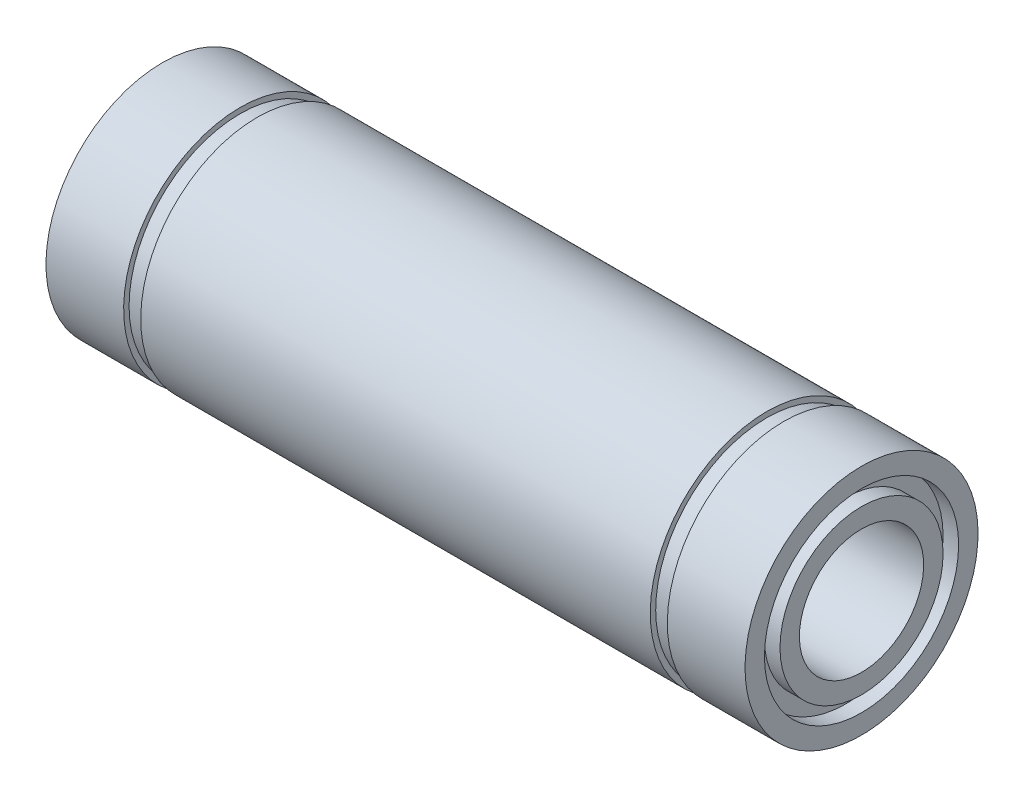
SolidWorks part; units mm, degrees
material "Ст3сп ГОСТ 535-2005"
ref_plane "Plano frontal" through (0, 0, 0) normal (0, 0, 1) x (1, 0, 0)
ref_plane "Plano superior" through (0, 0, 0) normal (0, 1, 0) x (1, 0, 0)
ref_plane "Plano direito" through (0, 0, 0) normal (1, 0, 0) x (0, 0, -1)
sketch "Esboço1" plane through (0, 0, 0) normal (0, 0, 1) x (1, 0, 0)
  line L0 (-22.5, 7.5) -> (-17.5, 7.5)
  line L1 (-17.5, 7.5) -> (-17.5, 7.15)
  line L2 (-17.5, 7.15) -> (-16.4, 7.15)
  line L3 (-16.4, 7.15) -> (-16.4, 7.5)
  line L4 (-16.4, 7.5) -> (16.4, 7.5)
  line L5 (16.4, 7.5) -> (16.4, 7.15)
  line L6 (16.4, 7.15) -> (17.5, 7.15)
  line L7 (17.5, 7.15) -> (17.5, 7.5)
  line L8 (17.5, 7.5) -> (22.5, 7.5)
  line L9 (22.5, 7.5) -> (22.5, 6.25)
  line L10 (22.5, 4) -> (-22.5, 4)
  line L11 (-22.5, 4) -> (-22.5, 5.25)
  line L12 (0, 4) -> (0, 0) construction
  line L13 (0, 0) -> (-86.5, 0) construction
  line L14 (-22.5, 6.25) -> (-22.5, 7.5)
  line L15 (-22.5, 6.25) -> (-21.5, 6.25)
  line L16 (22.5, 5.25) -> (22.5, 4)
  line L17 (-21.5, 6.25) -> (-21.5, 5.25)
  line L18 (-21.5, 5.25) -> (-22.5, 5.25)
  line L19 (22.5, 6.25) -> (21.5, 6.25)
  line L21 (22.5, 5.25) -> (21.5, 5.25)
  line L22 (21.5, 6.25) -> (21.5, 5.25)
  dimension "D1" = 45
  dimension "D2" = 35
  dimension "D3" = 1.1
  dimension "D4" = 8
  dimension "D5" = 15
  dimension "D6" = 14.3
  dimension "D7" = 1
  dimension "D8" = 1
  dimension "D9" = 1
  dimension "D10" = 1
revolve "Revolução1" add sketch "Esboço1" angle 360 about L13
